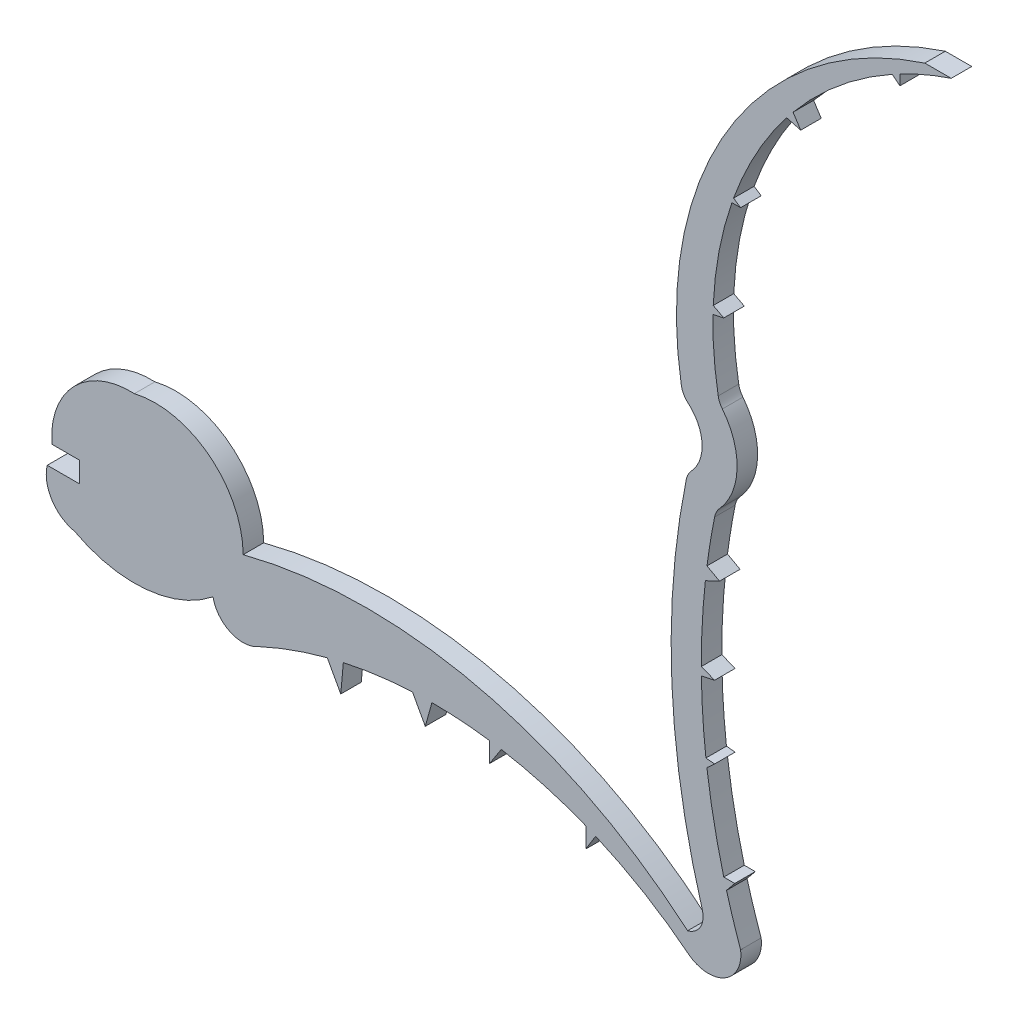
SolidWorks part; units mm, degrees
ref_plane "Front Plane" through (0, 0, 0) normal (0, 0, 1) x (1, 0, 0)
ref_plane "Top Plane" through (0, 0, 0) normal (0, 1, 0) x (1, 0, 0)
ref_plane "Right Plane" through (0, 0, 0) normal (1, 0, 0) x (0, 0, -1)
sketch "Sketch1" plane through (0, 0, 0) normal (0, 0, 1) x (1, 0, 0)
  line L0 (12.8014, 0) -> (12.8014, -1.524)
  line L1 (12.8014, -1.524) -> (10.3919, -1.524)
  line L2 (75.5439, 56.9103) -> (77.5055, 56.9103)
  line L3 (12.8014, 0) -> (10.7293, 0)
  line L4 (10.7293, 0) -> (10.7293, 0.8123)
  line L5 (31.1819, -3.5065) -> (32.184, -5.3359)
  line L6 (32.184, -5.3359) -> (32.3737, -3.2195)
  line L7 (43.2347, -2.8063) -> (43.2347, -4.2777)
  line L8 (37.5058, -2.5396) -> (38.458, -4.2777)
  line L9 (38.458, -4.2777) -> (38.9509, -2.5055)
  line L10 (43.2347, -4.2777) -> (44.1016, -2.9414)
  line L11 (50.3749, -4.7141) -> (50.3749, -6.2061)
  line L12 (50.3749, -6.2061) -> (51.1063, -5.019)
  line L13 (60.8222, -3.641) -> (61.4329, -2.8903)
  line L14 (61.4329, -2.8903) -> (60.618, -2.8903)
  line L15 (59.3645, 3.5199) -> (59.9388, 4.0441)
  line L16 (59.9388, 4.0441) -> (59.2927, 4.1031)
  line L17 (58.9551, 9.2202) -> (59.9388, 9.4267)
  line L18 (59.9388, 9.4267) -> (58.9497, 9.8136)
  line L19 (59.3719, 16.4956) -> (60.3043, 15.9798)
  line L20 (60.3043, 15.9798) -> (59.2505, 15.4838)
  line L21 (59.8167, 32.8896) -> (60.618, 33.0608)
  line L22 (60.618, 33.0608) -> (59.8355, 33.4698)
  line L23 (61.223, 40.7776) -> (61.8686, 40.7776)
  line L24 (61.8686, 40.7776) -> (61.3459, 41.1263)
  line L25 (65.2857, 48.2685) -> (66.3293, 47.9881)
  line L26 (66.3293, 47.9881) -> (65.7635, 48.8631)
  line L27 (73.1239, 54.9797) -> (73.6934, 54.521)
  line L28 (73.6934, 54.521) -> (73.6934, 55.2872)
  arc A0 (10.3919, -1.524) -> (12.438, -4.7634) centre (12.9851, -2.152) ccw
  arc A1 (12.438, -4.7634) -> (22.6974, -3.832) centre (16.8612, 3.4846) ccw
  arc A2 (24.9371, 0) -> (57.9333, -7.6836) centre (34.094, -35.3679) cw
  arc A3 (58.0982, -9.2224) -> (61.8686, -6.9356) centre (59.484, -7.2556) ccw
  arc A4 (61.8686, -6.9356) -> (60.8222, -3.641) centre (109.4155, 9.9795) cw
  arc A5 (59.0209, -5.7722) -> (57.9333, -7.6836) centre (57.56, -6.2061) cw
  arc A6 (58.2177, 22.0233) -> (57.9824, 26.2499) centre (56.0907, 24.0248) ccw
  arc A7 (60.3043, 20.6471) -> (60.5136, 27.1562) centre (56.5821, 24.0248) ccw
  arc A8 (57.4663, 27.1601) -> (75.5439, 56.9103) centre (83.7614, 31.5494) cw
  arc A9 (77.5055, 56.9103) -> (73.6934, 55.2872) centre (85.7147, 32.3417) ccw
  arc A10 (57.8343, 21.2833) -> (59.0209, -5.7722) centre (112.5653, 10.13) ccw
  arc A11 (22.6974, -3.832) -> (26.0866, -5.3359) centre (24.9215, -3.3908) ccw
  arc A12 (24.9371, 0) -> (16.8612, 6.3137) centre (18.4035, -0.0354) ccw
  arc A13 (16.8612, 6.3137) -> (10.7293, 0.8123) centre (16.589, 0.4491) ccw
  arc A14 (58.2177, 22.0233) -> (57.8343, 21.2833) centre (59.3276, 20.979) ccw
  arc A15 (59.9388, 19.9233) -> (60.3043, 20.6471) centre (61.4329, 19.623) cw
  arc A16 (60.5136, 27.1562) -> (60.2049, 27.8409) centre (61.7057, 28.1057) cw
  arc A17 (57.9824, 26.2499) -> (57.4663, 27.1601) centre (58.9695, 27.411) cw
  arc A18 (26.0866, -5.3359) -> (31.1819, -3.5065) centre (38.9509, -33.1546) cw
  arc A19 (32.3737, -3.2195) -> (37.5058, -2.5396) centre (38.9509, -33.1546) cw
  arc A20 (38.9509, -2.5055) -> (43.2347, -2.8063) centre (38.9509, -33.1546) cw
  arc A21 (44.1016, -2.9414) -> (50.3749, -4.7141) centre (38.9509, -33.1546) cw
  arc A22 (51.1063, -5.019) -> (58.0982, -9.2224) centre (38.9509, -33.1546) cw
  arc A23 (60.618, -2.8903) -> (59.3645, 3.5199) centre (109.4155, 9.9795) cw
  arc A24 (59.2927, 4.1031) -> (58.9551, 9.2202) centre (109.4155, 9.9795) cw
  arc A25 (58.9497, 9.8136) -> (59.2505, 15.4838) centre (109.4155, 9.9795) cw
  arc A26 (59.3719, 16.4956) -> (59.9388, 19.9233) centre (109.4155, 9.9795) cw
  arc A27 (73.1239, 54.9797) -> (65.7635, 48.8631) centre (85.7147, 32.3417) ccw
  arc A28 (65.2857, 48.2685) -> (61.3459, 41.1263) centre (85.7147, 32.3417) ccw
  arc A29 (61.223, 40.7776) -> (59.8355, 33.4698) centre (85.7147, 32.3417) ccw
  arc A30 (59.8167, 32.8896) -> (60.2049, 27.8409) centre (85.7147, 32.3417) ccw
  spline S0 degree 3 poles (4.3256, -6.7245) (6.9485, -5.7185) (9.7751, -5.0539) (14.32, -4.555) (15.886, -4.4721) (18.3122, -4.4737) (19.1358, -4.4954) (20.7975, -4.5807) (21.6352, -4.6441) (22.4796, -4.7277) knots 0 0 0 0 0.5 0.5 0.75 0.75 0.875 0.875 1 1 1 1 construction
  spline S1 degree 3 poles (3.0037, -3.6141) (4.7276, -3.2763) (6.627, -3.0729) (9.7229, -2.9499) (10.7963, -2.9394) (12.4684, -2.9674) (13.0362, -2.984) (14.1925, -3.0315) (14.7825, -3.0626) (17.7585, -3.251) (20.2353, -3.5077) (24.0887, -4.0151) (25.3963, -4.2048) (28.0588, -4.6195) (29.4163, -4.8451) (30.7867, -5.0836) knots 0 0 0 0 0.25 0.25 0.375 0.375 0.4375 0.4375 0.5 0.5 0.75 0.75 0.875 0.875 1 1 1 1 construction
  spline S2 degree 3 poles (11.3688, -5.1107) (14.1284, -4.1892) (16.5484, -3.5694) (19.1581, -3.1539) (19.6591, -3.0888) (20.6187, -2.9947) (21.0778, -2.9655) (22.387, -2.932) (23.1623, -2.9816) (23.8421, -3.0979) knots 0 0 0 0 0.5 0.5 0.625 0.625 0.75 0.75 1 1 1 1 construction
  dimension "D1" = 1.524
  dimension "D2" = 1.524
extrude "Boss-Extrude1" add sketch "Sketch1" along normal blind 1.524
